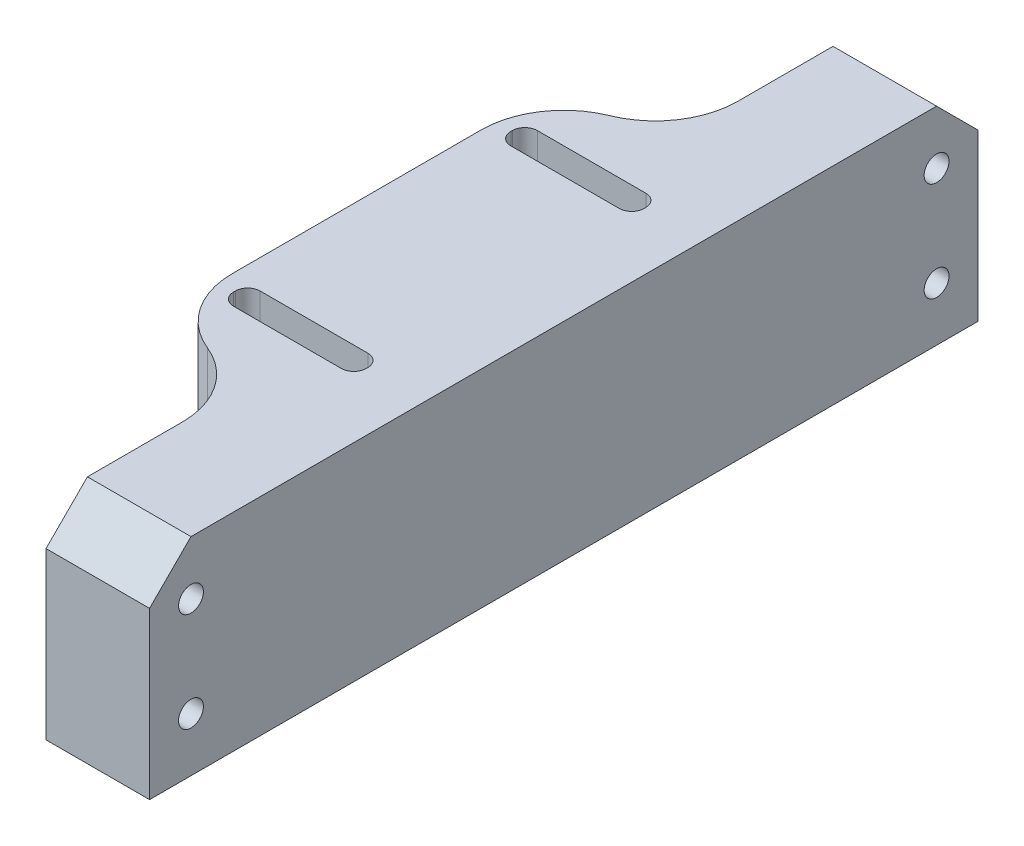
SolidWorks part; units mm, degrees
ref_plane "Спереди" through (0, 0, 0) normal (0, 0, 1) x (1, 0, 0)
ref_plane "Сверху" through (0, 0, 0) normal (0, 1, 0) x (1, 0, 0)
ref_plane "Справа" through (0, 0, 0) normal (1, 0, 0) x (0, 0, -1)
sketch "Эскиз1" plane through (0, 0, 0) normal (0, 1, 0) x (1, 0, 0)
  line L0 (-12.5, 16.75) -> (12.5, 16.75) construction
  line L1 (-12.5, -25) -> (0, -25)
  line L2 (0, -25) -> (0, -50)
  line L3 (0, -50) -> (12.5, -50)
  line L4 (-12.5, -25) -> (-12.5, 25)
  line L5 (12.5, -25) -> (-12.5, 25) construction
  line L6 (12.5, 25) -> (-12.5, -25) construction
  line L7 (-12.5, -16.75) -> (12.5, -16.75) construction
  line L8 (0, 25) -> (0, -25) construction
  line L9 (-2.5, -25) -> (-2.5, 25) construction
  line L11 (5.5, -15.15) -> (-10.5, -15.15)
  line L12 (5.5, -15.15) -> (5.5, -18.35)
  line L13 (5.5, -18.35) -> (-10.5, -18.35)
  line L14 (-10.5, -15.15) -> (-10.5, -18.35)
  line L15 (5.5, -15.15) -> (-10.5, -18.35) construction
  line L16 (5.5, -18.35) -> (-10.5, -15.15) construction
  line L17 (5.5477, 18.35) -> (-10.5477, 18.35)
  line L18 (5.5477, 18.35) -> (5.5477, 15.15)
  line L19 (5.5477, 15.15) -> (-10.5477, 15.15)
  line L20 (-10.5477, 18.35) -> (-10.5477, 15.15)
  line L21 (5.5477, 18.35) -> (-10.5477, 15.15) construction
  line L22 (5.5477, 15.15) -> (-10.5477, 18.35) construction
  line L23 (0, 25) -> (0, 50)
  line L24 (0, 50) -> (12.5, 50)
  line L25 (12.5, -50) -> (12.5, 50)
  line L26 (0, 25) -> (-12.5, 25)
  line L27 (12.5, 25) -> (-12.5, 25) construction
  line L28 (-12.5, -25) -> (12.5, -25) construction
  point P0 (0, 0)
  point P10 (0, 16.75)
  point P13 (-2.5, -16.75)
  point P15 (0, -16.75)
  point P19 (-2.5, 16.75)
  point P23 (0, 0)
  dimension "D1" = 10
  dimension "D2" = 3.2
  dimension "D3" = 25
  dimension "D4" = 33.5
  dimension "D5" = 50
  dimension "D6" = 100
  dimension "D7" = 16
extrude "Бобышка-Вытянуть1" add sketch "Эскиз1" along normal blind 25
sketch "Эскиз2" plane through (0, 0, 0) normal (-1, 0, 0) x (0, 0, 1)
  line L0 (-45, 0) -> (-45, 25) construction
  line L2 (-50, 0) -> (-25, 0) construction
  line L3 (-50, 25) -> (-25, 25) construction
  circle A0 centre (-45, 6.5) radius 1.5
  circle A1 centre (-45, 18.5) radius 1.5
  point P11 (-45, 12.5)
  dimension "D1" = 12
  dimension "D3" = 3
  dimension "D2" = 6
  dimension "D4" = 5
extrude "Вырез-Вытянуть1" cut sketch "Эскиз2" against normal through all
sketch "Эскиз3" plane through (0, 0, 0) normal (-1, 0, 0) x (0, 0, 1)
  line L0 (45, 0) -> (45, 25) construction
  line L3 (25, 0) -> (50, 0) construction
  line L4 (25, 25) -> (50, 25) construction
  circle A0 centre (45, 6.5) radius 1.5
  circle A1 centre (45, 18.5) radius 1.5
  point P10 (45, 12.5)
  dimension "D3" = 3
  dimension "D1" = 12
  dimension "D2" = 6
  dimension "D4" = 5
extrude "Вырез-Вытянуть2" cut sketch "Эскиз3" against normal through all
fillet "Скругление6" radius 10 2 edges at (-12.5, 12.5, 25) (-12.5, 12.5, -25)
fillet "Скругление7" radius 1.5 8 edges at (5.5, 12.5, 15.15) (5.5, 12.5, 18.35) (-10.5, 12.5, 18.35) (-10.5, 12.5, 15.15) (-10.5477, 12.5, -15.15) (-10.5477, 12.5, -18.35) (5.5477, 12.5, -18.35) (5.5477, 12.5, -15.15)
chamfer "Фаска1" distance 5 angle 45 2 edges at (6.25, 25, 50) (6.25, 25, -50)
fillet "Скругление8" radius 10 2 edges at (0, 12.5, 25) (0, 12.5, -25)
sketch "Sketch1" plane through (0, 0, 0) normal (0, -1, 0) x (1, 0, 0)
  line L0 (-12.5, 20.75) -> (8.5, 20.75)
  line L1 (-12.5, -15) -> (-12.5, 15) construction
  line L2 (12.5, 50) -> (12.5, -50) construction
  line L3 (8.5, 20.75) -> (8.5, 12.75)
  line L4 (-12.5, 12.75) -> (-12.5, 20.75)
  line L5 (8.5, 12.75) -> (-12.5, 12.75)
  line L6 (-12.5, -12.75) -> (8.5, -12.75)
  line L7 (8.5, -12.75) -> (8.5, -20.75)
  line L8 (8.5, -20.75) -> (-12.5, -20.75)
  line L9 (-12.5, -20.75) -> (-12.5, -12.75)
  line L10 (-12.5, 16.75) -> (14, 16.75) construction
  line L11 (0.75, 18.35) -> (0.75, 15.15) construction
  line L14 (-12.5, -16.75) -> (14, -16.75) construction
  line L15 (-9, 18.35) -> (4, 18.35) construction
  line L16 (0.75, -15.15) -> (0.75, -18.35) construction
  line L19 (4, 15.15) -> (-9, 15.15) construction
  line L20 (4.0477, -18.35) -> (-9.0477, -18.35) construction
  line L21 (-9.0477, -15.15) -> (4.0477, -15.15) construction
  point P22 (0.75, 16.75)
  point P23 (0.75, 16.75)
  point P25 (0.75, -16.75)
  point P33 (0.75, -16.75)
  dimension "D1" = 4
  dimension "D2" = 8
extrude "Cut-Extrude1" cut sketch "Sketch1" against normal blind 7
